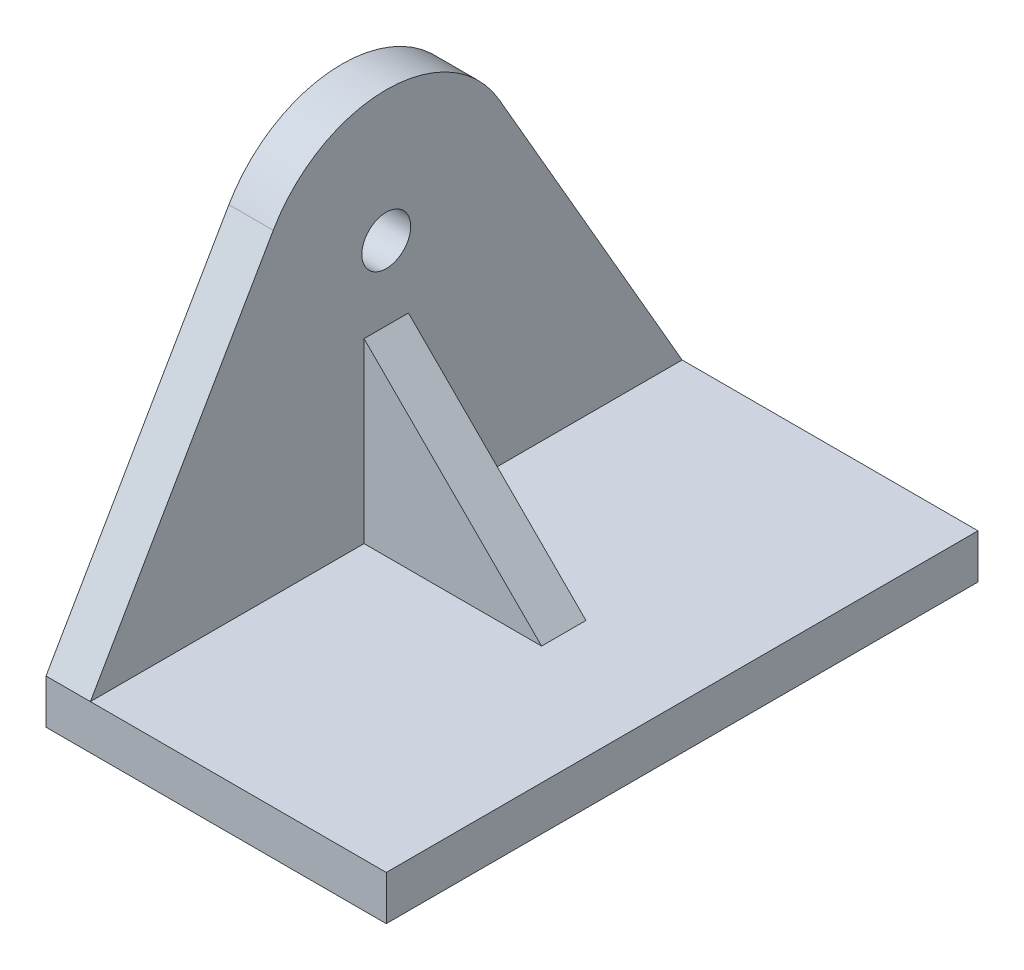
SolidWorks part; units mm, degrees
ref_plane "前视基准面" through (0, 0, 0) normal (0, 0, 1) x (1, 0, 0)
ref_plane "上视基准面" through (0, 0, 0) normal (0, 1, 0) x (1, 0, 0)
ref_plane "右视基准面" through (0, 0, 0) normal (1, 0, 0) x (0, 0, -1)
other "Configuration Table"
sketch "草图1" plane through (0, 0, 0) normal (1, 0, 0) x (0, 0, -1)
  line L0 (-20, 0) -> (20, 0)
  line L1 (-20, 0) -> (-20, 3)
  line L2 (-20, 3) -> (-7.6388, 24.4103)
  line L3 (20, 0) -> (20, 3)
  line L4 (20, 3) -> (7.6388, 24.4103)
  arc A0 (7.6388, 24.4103) -> (-7.6388, 24.4103) centre (0, 20) ccw
  point P6 (-7.6388, 24.4103)
  point P12 (7.6388, 24.4103)
  dimension "D1" = 40
  dimension "D2" = 3
extrude "凸台-拉伸1" add sketch "草图1" against normal blind 3
sketch "草图2" plane through (0, 0, 0) normal (1, 0, 0) x (0, 0, -1)
  line L0 (0, 0) -> (0, 20) construction
  circle A0 centre (0, 20) radius 1.65
  dimension "D2" = 3.3
  dimension "D1" = 20
extrude "切除-拉伸1" cut sketch "草图2" against normal through all
sketch "草图3" plane through (0, 0, 0) normal (1, 0, 0) x (0, 0, -1)
  line L1 (-20, 3) -> (20, 3)
  line L2 (-20, 3) -> (-20, 0)
  line L3 (-20, 0) -> (20, 0)
  line L4 (20, 3) -> (20, 0)
extrude "凸台-拉伸2" add sketch "草图3" along normal blind 20
sketch "草图4" plane through (0, 0, 0) normal (0, 0, 1) x (1, 0, 0)
  line L0 (0, 3) -> (0, 15)
  line L1 (0, 24.4103) -> (0, 3) construction
  line L2 (0, 15) -> (12, 3)
  line L3 (20, 3) -> (0, 3) construction
  line L4 (12, 3) -> (0, 3)
  dimension "D1" = 12
  dimension "D2" = 12
extrude "凸台-拉伸3" add sketch "草图4" along normal mid plane 3
